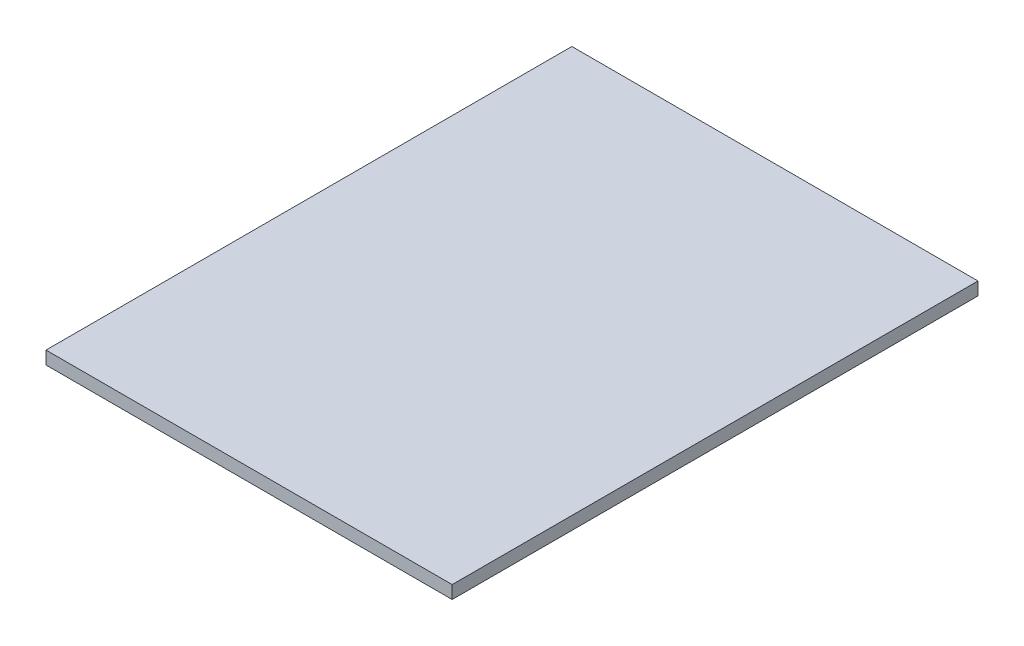
SolidWorks part; units mm, degrees
material "Oak"
ref_plane "Front Plane" through (0, 0, 0) normal (0, 0, 1) x (1, 0, 0)
ref_plane "Top Plane" through (0, 0, 0) normal (0, 1, 0) x (1, 0, 0)
ref_plane "Right Plane" through (0, 0, 0) normal (1, 0, 0) x (0, 0, -1)
sketch "Sketch1" plane through (0, 0, 0) normal (0, 1, 0) x (1, 0, 0)
  line L1 (0, 0) -> (517.4488, 0)
  line L2 (0, 0) -> (0, 669.925)
  line L3 (0, 669.925) -> (517.4488, 669.925)
  line L4 (517.4488, 0) -> (517.4488, 669.925)
  dimension "D1" = 669.925
  dimension "D2" = 517.4488
extrude "Boss-Extrude1" add sketch "Sketch1" along normal blind 19.05
chamfer "Chamfer1" distance 2.54 angle 45 4 edges at (258.7244, 0, 0) (517.4488, 0, -334.9625) (258.7244, 0, -669.925) (0, 0, -334.9625)
